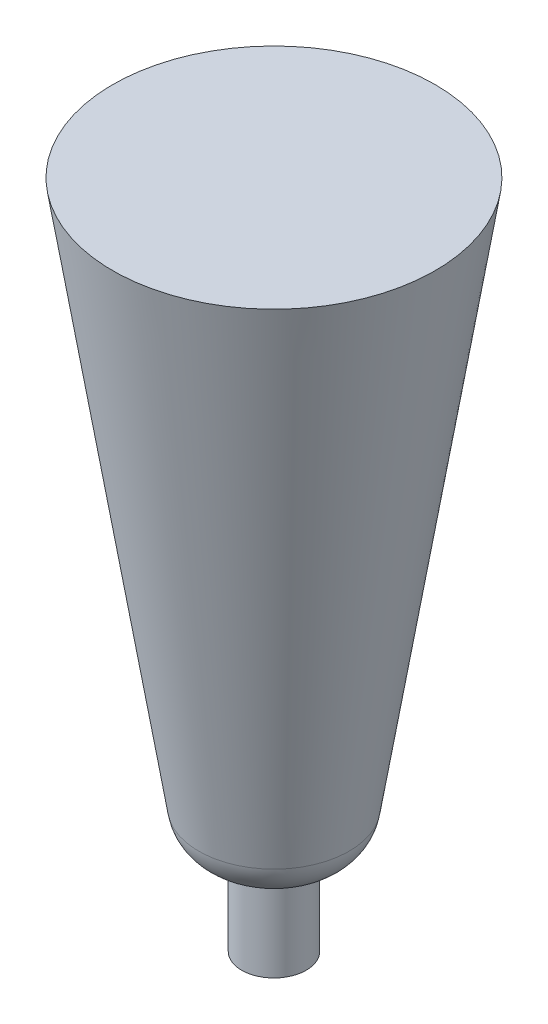
SolidWorks part; units mm, degrees
ref_plane "Front Plane" through (0, 0, 0) normal (0, 0, 1) x (1, 0, 0)
ref_plane "Top Plane" through (0, 0, 0) normal (0, 1, 0) x (1, 0, 0)
ref_plane "Right Plane" through (0, 0, 0) normal (1, 0, 0) x (0, 0, -1)
sketch "Sketch2" plane through (0, 0, 0) normal (0, 0, 1) x (1, 0, 0)
  line L0 (0, 0) -> (0, 83.5535) construction
  line L1 (0, 0) -> (3.81, 0)
  line L2 (3.81, 0) -> (3.81, 10.16)
  line L16 (8.8674, 14.6804) -> (9.1362, 16.3866)
  line L17 (9.1362, 16.3866) -> (19, 79)
  line L21 (0, 79) -> (19, 79)
  line L24 (0, 0) -> (0, 79)
  arc A1 (3.81, 10.16) -> (8.8674, 14.6804) centre (3.5729, 15.5145) ccw
  dimension "D3" = 19
  dimension "D1" = 3.81
  dimension "D2" = 10.16
  dimension "D4" = 79
revolve "Revolve6" add sketch "Sketch2" angle 360 about L0
